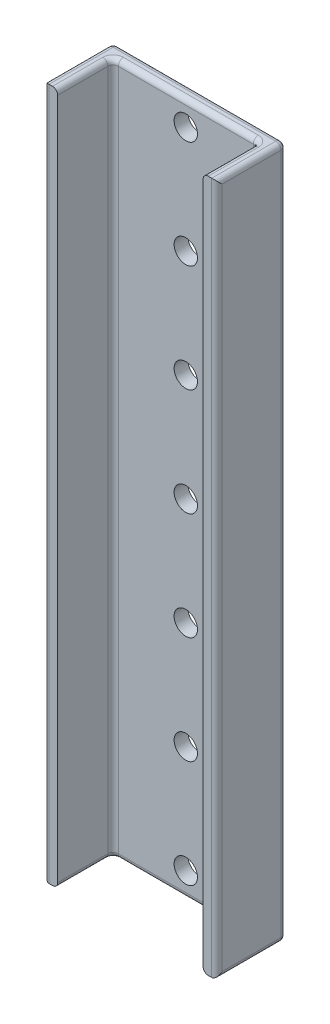
SolidWorks part; units mm, degrees
ref_plane "Alzado" through (0, 0, 0) normal (0, 0, 1) x (1, 0, 0)
ref_plane "Planta" through (0, 0, 0) normal (0, 1, 0) x (1, 0, 0)
ref_plane "Vista lateral" through (0, 0, 0) normal (1, 0, 0) x (0, 0, -1)
sketch "Croquis1" plane through (0, 0, 0) normal (0, 1, 0) x (1, 0, 0)
  line L0 (0, 0) -> (0, 40) construction
  line L1 (0, 0) -> (-50, 0) construction
  line L2 (47, 40) -> (-47, 40)
  line L3 (-50, 37) -> (-50, 0)
  line L4 (50, 37) -> (50, 0)
  arc A0 (-47, 40) -> (-50, 37) centre (-47, 37) ccw
  arc A1 (47, 40) -> (50, 37) centre (47, 37) cw
  point P1 (-8, 0)
  point P6 (0, 7.4254)
  point P8 (-50.6138, 0)
  dimension "D3" = 3
  dimension "D1" = 40
  dimension "D2" = 100
extrude "Extruir-Lámina1" add sketch "Croquis1" along normal blind 400 thin
fillet "Redondeo1" radius 3 2 edges at (42, 200, -32) (-42, 200, -32)
fillet "Redondeo2" radius 3 22 edges at (-49.1213, 400, -39.1213) (49.1213, 400, -39.1213) (-49.1213, 0, -39.1213) (49.1213, 0, -39.1213) (-42, 400, -14.5) (-41.1213, 400, -31.1213) (42, 400, -14.5) (41.1213, 400, -31.1213) (-42, 0, -14.5) (-41.1213, 0, -31.1213) (42, 0, -14.5) (41.1213, 0, -31.1213) (0, 400, -40) (0, 0, -40) (-50, 400, -18.5) (-50, 200, 0) (-50, 0, -18.5) (50, 200, 0) (50, 400, -18.5) (50, 0, -18.5) (0, 400, -32) (0, 0, -32)
sketch "Croquis2" plane through (0, 0, -40) normal (0, 0, -1) x (-1, 0, 0)
  line L0 (-50, 397) -> (-50, 3) construction
  line L1 (0, 200) -> (-50, 200) construction
  point P0 (0, 386)
  point P1 (0, 324)
  point P2 (0, 262)
  point P3 (0, 200)
  point P4 (0, 138)
  point P7 (-50, 200)
  point P8 (0, 76)
  point P10 (0, 14)
  dimension "D1" = 62
  dimension "D2" = 62
  dimension "D3" = 62
hole_wizard "Taladro de margen para M121" positions "Croquis2" profile "Croquis3" hole size "M12" standard "Ansi Metric" end condition through all
sketch "Croquis3" plane through (0, 386, -40) normal (1, 0, 0) x (0, 1, 0)
  line L0 (0, 0) -> (0, 40)
  line L1 (0, 40) -> (6.75, 40)
  line L2 (6.75, 40) -> (6.75, 0)
  line L5 (6.75, 0) -> (0, 0)
  line L11 (0, -6.35) -> (0, 107.95) construction
  dimension "Diámetro de taladro hasta el siguiente" = 13.5
  dimension "Profundidad de taladro hasta el siguiente" = 40
equation "\"D2@Croquis2\"=\"D1@Croquis2\""
equation "\"D3@Croquis2\"=\"D1@Croquis2\""
